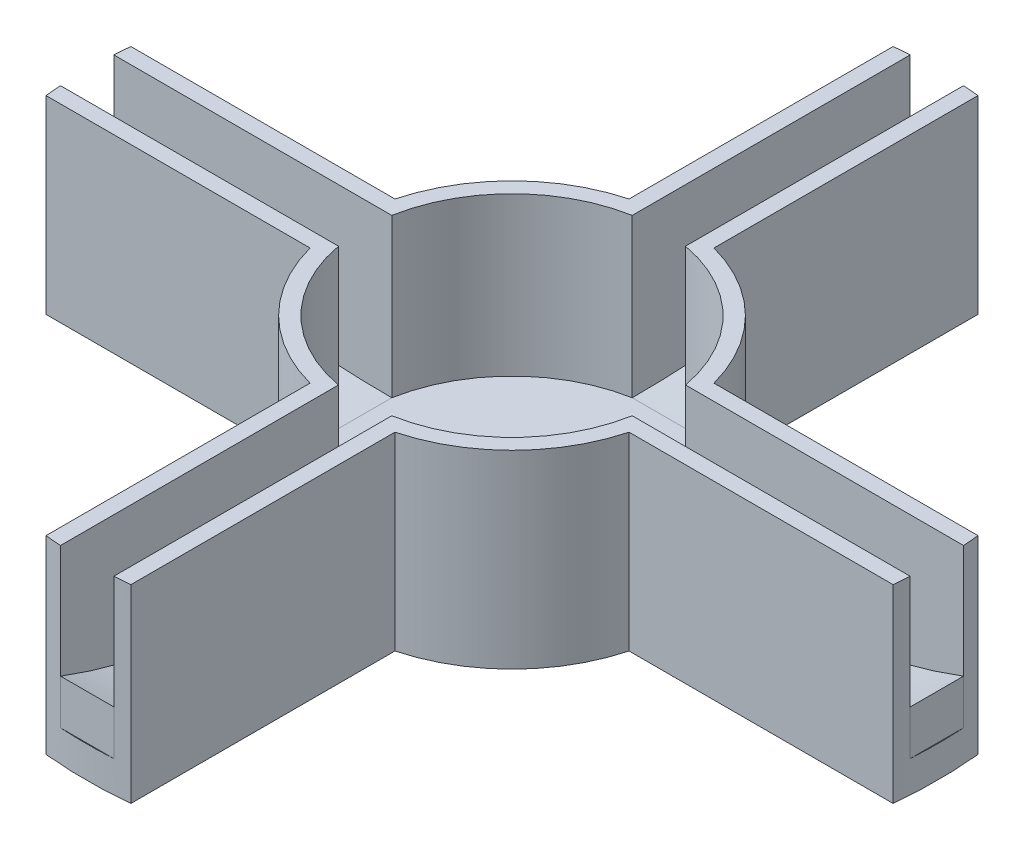
SolidWorks part; units mm, degrees
other "Markup1"
sketch "Sketch5" plane through (34.95, 15, 34.95) normal (0.0371, 0.9957, 0.0854) x (0.9174, 0, -0.3981)
ref_plane "Front Plane" through (0, 0, 0) normal (0, 0, 1) x (1, 0, 0)
ref_plane "Top Plane" through (0, 0, 0) normal (0, 1, 0) x (1, 0, 0)
ref_plane "Right Plane" through (0, 0, 0) normal (1, 0, 0) x (0, 0, -1)
sketch "Sketch2" plane through (0, 0, 0) normal (0, 1, 0) x (1, 0, 0)
  circle A0 centre (0, 0) radius 9.45
  circle A1 centre (0, 0) radius 26.95
  dimension "D1" = 18.9
  dimension "D2" = 17.5
extrude "Boss-Extrude2" add sketch "Sketch2" along normal blind 10 contours A1 A0
sketch "Sketch3" plane through (0, 0, 0) normal (0, -1, 0) x (1, 0, 0)
  circle A0 centre (0, 0) radius 26.95 construction
  circle A1 centre (0, 0) radius 26.95
extrude "Boss-Extrude3" add sketch "Sketch3" along normal blind 2
sketch "Sketch4" plane through (0, 10, 0) normal (0, 1, 0) x (1, 0, 0)
  line L0 (-1.6875, 26.8971) -> (-1.6875, 9.2981)
  line L1 (1.6875, 9.2981) -> (1.6875, 26.8971)
  line L2 (0, 0) -> (0, 24.9078) construction
  line L3 (-1.6875, 36.1723) -> (1.6875, 36.1723) construction
  circle A0 centre (0, 0) radius 26.95 construction
  circle A1 centre (0, 0) radius 9.45 construction
  arc A2 (1.6875, 26.8971) -> (-1.6875, 26.8971) centre (0, 0) ccw
  arc A3 (1.6875, 9.2981) -> (-1.6875, 9.2981) centre (0, 0) ccw
  arc A4 (-1.6875, 26.8971) -> (1.6875, 26.8971) centre (0, 0) ccw construction
  arc A5 (-1.6875, 9.2981) -> (1.6875, 9.2981) centre (0, 0) ccw construction
  point P11 (0, 36.1723)
  dimension "D1" = 3.375
extrude "Cut-Extrude1" cut sketch "Sketch4" against normal up to surface (10 mm away) up to face at (0, 0, 9.45)
sketch "Sketch7" plane through (-1.6875, 0, 0) normal (1, 0, 0) x (0, 0, -1)
  line L0 (9.2981, 0) -> (9.2981, 10) construction
  line L2 (26.8971, 0) -> (26.8971, 10) construction
  line L3 (26.8971, 0) -> (26.8971, 2.834)
  line L4 (26.8971, 0) -> (9.2981, 0) construction
  line L5 (26.8971, 0) -> (9.2981, 0)
  line L6 (26.8971, 2.834) -> (26.8971, 10) construction
  ellipse E0 centre (9.2981, 10.16) end of major axis (34.6981, 10.16) minor radius 10.16 (9.2981, 0) -> (26.8971, 2.834) ccw
  ellipse E1 centre (9.2981, 10.16) end of major axis (34.6981, 10.16) minor radius 10.16 (26.8971, 2.834) -> (9.2981, 0) ccw construction
  dimension "D1" = 25.4
  dimension "D2" = 10.16
extrude "Boss-Extrude4" add sketch "Sketch7" along normal up to next (3.375 mm away)
pattern_circular "CirPattern1" count 4 over 360 about axis through (0, 10, 0) along (0, -1, 0) of "Cut-Extrude1", "Boss-Extrude4"
sketch "Sketch6" plane through (0, 10, 0) normal (0, 1, 0) x (1, 0, 0)
  line L0 (-26.8157, 2.6875) -> (-10.0985, 2.6875)
  line L1 (-9.2981, 1.6875) -> (-26.8971, 1.6875) construction
  line L2 (-2.6875, 26.8157) -> (-2.6875, 10.0985)
  line L3 (-1.6875, 26.8971) -> (-1.6875, 9.2981) construction
  arc A0 (-1.6875, 26.8971) -> (-26.8971, 1.6875) centre (0, 0) ccw construction
  arc A1 (-2.6875, 26.8157) -> (-26.8157, 2.6875) centre (0, 0) ccw
  arc A2 (-2.6875, 10.0985) -> (-10.0985, 2.6875) centre (0, 0) ccw
  arc A3 (-1.6875, 9.2981) -> (-9.2981, 1.6875) centre (0, 0) ccw construction
  arc A4 (-10.0985, 2.6875) -> (-2.6875, 10.0985) centre (0, 0) ccw construction
  dimension "D3" = 1
  dimension "D1" = 1
  dimension "D2" = 1
extrude "Cut-Extrude2" cut sketch "Sketch6" against normal up to surface (12 mm away) up to face at (0, -2, -26.95)
pattern_circular "CirPattern2" count 4 over 360 about axis through (0, 0, 0) along (0, 1, 0) of "Cut-Extrude2"
equation "\"B_OD\" = 18.7mm"
equation "\"B_ID\" = 18mm"
equation "\"B_LG\" = 9in"
equation "\"F_TH\" = 0.125in"
equation "\"C_TH\" = 0.125in"
equation "\"fins\" = 4"
equation "\"D1@Sketch2\"=\"B_OD\" + \"tol\""
equation "\"tol\" = 0.2mm"
equation "\"D1@Sketch4\"=\"F_TH\"+\"tol\""
equation "\"D1@CirPattern1\"=\"fins\""
equation "\"D1@CirPattern2\"=\"fins\""
